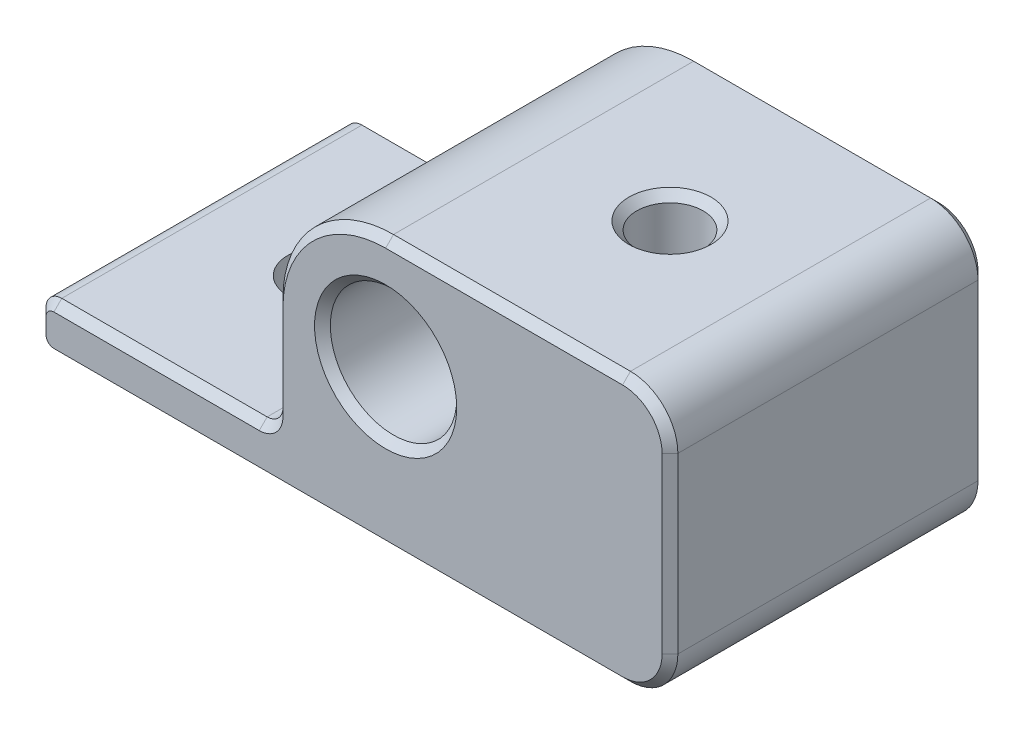
SolidWorks part; units mm, degrees
ref_plane "Front Plane" through (0, 0, 0) normal (0, 0, 1) x (1, 0, 0)
ref_plane "Top Plane" through (0, 0, 0) normal (0, 1, 0) x (1, 0, 0)
ref_plane "Right Plane" through (0, 0, 0) normal (1, 0, 0) x (0, 0, -1)
ref_plane "Plane1" through (0, -10, 0) normal (0, -1, 0) x (1, 0, 0)
sketch "Sketch1" plane through (0, -10, 0) normal (0, -1, 0) x (1, 0, 0)
  line L0 (18, 20) -> (-22, 20)
  line L1 (-22, 20) -> (-22, 0)
  line L2 (-22, 0) -> (18, 0)
  line L3 (18, 0) -> (18, 20)
extrude "Boss-Extrude1" add sketch "Sketch1" against normal blind 17
sketch "Sketch2" plane through (0, 0, 20) normal (0, 0, 1) x (1, 0, 0)
  line L0 (-22, 7) -> (-22, -7)
  line L1 (-22, -7) -> (-7, -7)
  line L2 (-7, -7) -> (-7, 7)
  line L3 (-7, 7) -> (-22, 7)
extrude "Cut-Extrude1" cut sketch "Sketch2" against normal through all
hole_wizard "Ø4.4 (4.4) Diameter Hole1" positions "Sketch4" profile "Sketch3" hole size "Ø4.4" standard "ANSI Metric"
sketch "Sketch4" plane through (0, -10, 0) normal (0, -1, 0) x (-1, 0, 0)
  point P0 (14, -10)
sketch "Sketch3" plane through (-14, -10, 10) normal (1, 0, 0) x (0, 0, -1)
  line L0 (0, 0) -> (0, 17)
  line L1 (0, 17) -> (2.2, 17)
  line L2 (2.2, 17) -> (2.2, 0)
  line L5 (2.2, 0) -> (0, 0)
  line L11 (0, -6.35) -> (0, 107.95) construction
  dimension "Thru Hole Dia." = 4.4
  dimension "Thru Hole Depth" = 17
hole_wizard "Ø4.2 (4.2) Diameter Hole1" positions "Sketch6" profile "Sketch5" hole size "Ø4.2" standard "ANSI Metric"
sketch "Sketch6" plane through (0, 7, 0) normal (0, 1, 0) x (1, 0, 0)
  point P0 (8, -10)
sketch "Sketch5" plane through (8, 7, 10) normal (1, 0, 0) x (0, 0, 1)
  line L0 (0, 0) -> (0, 17)
  line L1 (0, 17) -> (2.1, 17)
  line L2 (2.1, 17) -> (2.1, 0)
  line L5 (2.1, 0) -> (0, 0)
  line L11 (0, -6.35) -> (0, 107.95) construction
  dimension "Thru Hole Dia." = 4.2
  dimension "Thru Hole Depth" = 17
hole_wizard "Hole1" positions "Sketch8" profile "Sketch7" legacy
sketch "Sketch8" plane through (0, 0, 20) normal (0, 0, 1) x (1, 0, 0)
  point P0 (0, 0)
sketch "Sketch7" plane through (0, 0, 20) normal (1, 0, 0) x (0, -1, 0)
  line L0 (0, 0) -> (0, 20)
  line L1 (0, 20) -> (3, 20)
  line L2 (3, 20) -> (3, 19)
  line L3 (3, 19) -> (4, 18)
  line L4 (4, 18) -> (4, 0)
  line L5 (4, 0) -> (0, 0)
  line L6 (0, -6.13) -> (0, 109.2824) construction
  line L7 (-3, 19) -> (-4, 18) construction
  line L8 (0, 20) -> (-3, 20) construction
  dimension "Diameter" = 6
  dimension "Depth" = 20
  dimension "C-Drill Diameter" = 8
  dimension "C-Drill Depth" = 18
  dimension "C-Drill Angle" = 90
fillet "Fillet1" radius 1 3 edges at (-7, -7, 10) (-22, -7, 10) (-22, -10, 10)
fillet "Fillet2" radius 3 2 edges at (18, -10, 10) (18, 7, 10)
fillet "Fillet3" radius 7 1 edges at (-7, 7, 10)
chamfer "Chamfer1" distance 0.5 angle 45 27 edges at (-3, -10, 20) (-21.7071, -9.7071, 20) (17.1213, -9.1213, 20) (-22, -8.5, 20) (18, -1.5, 20) (-21.7071, -7.2929, 20) (17.1213, 6.1213, 20) (-14.5, -7, 20) (7.5, 7, 20) (-7.2929, -6.7071, 20) (-4.9497, 4.9497, 20) (-7, -3, 20) (-22, -8.5, 0) (-21.7071, -9.7071, 0) (-21.7071, -7.2929, 0) (-3, -10, 0) (-14.5, -7, 0) (17.1213, -9.1213, 0) (-7.2929, -6.7071, 0) (18, -1.5, 0) (-7, -3, 0) (17.1213, 6.1213, 0) (-4.9497, 4.9497, 0) (7.5, 7, 0) (8, -10, 12.1) (4, 0, 20) (8, 7, 12.1)
